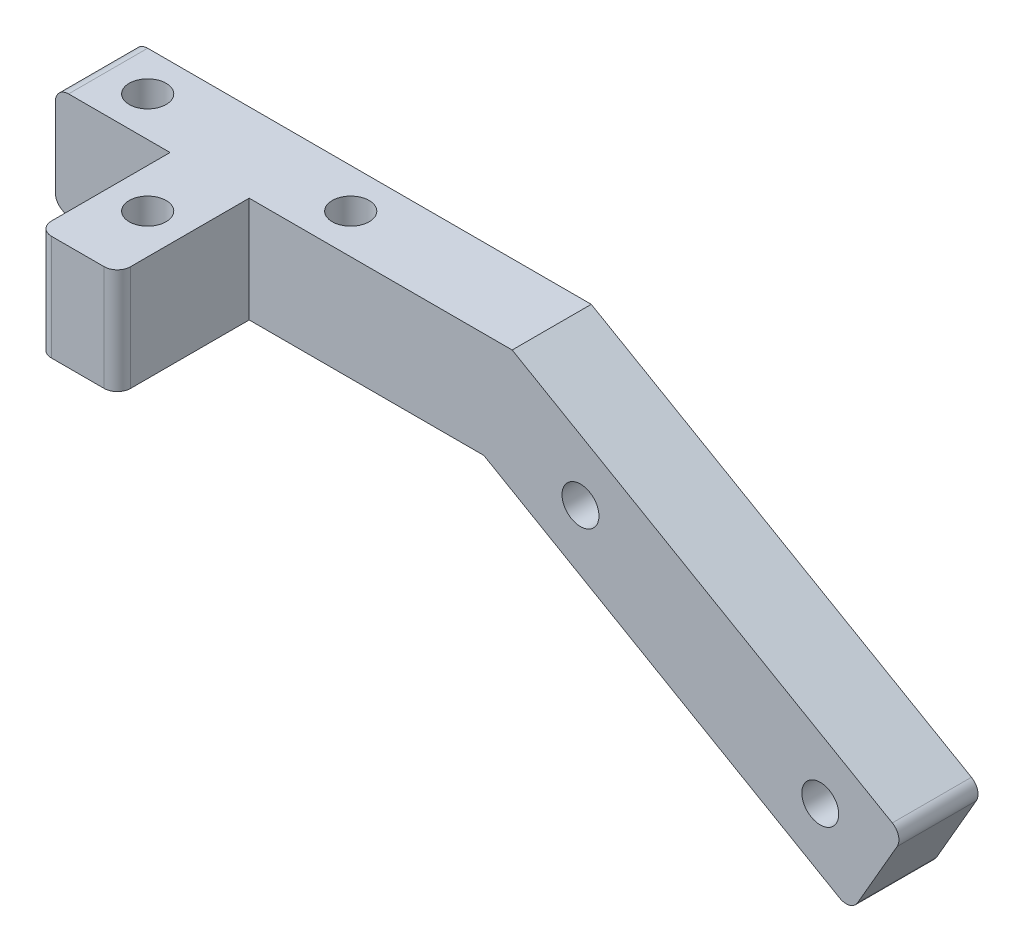
SolidWorks part; units mm, degrees
material "Copper"
ref_plane "Front Plane" through (0, 0, 0) normal (0, 0, 1) x (1, 0, 0)
ref_plane "Top Plane" through (0, 0, 0) normal (0, 1, 0) x (1, 0, 0)
ref_plane "Right Plane" through (0, 0, 0) normal (1, 0, 0) x (0, 0, -1)
sketch "Sketch1" plane through (0, 0, 0) normal (0, 0, 1) x (1, 0, 0)
  line L0 (0, 0) -> (0, 10.16)
  line L1 (0, 10.16) -> (43.9974, 10.16)
  line L2 (43.9974, 10.16) -> (81.7148, -11.6162)
  line L3 (81.7148, -11.6162) -> (76.6348, -20.415)
  line L4 (76.6348, -20.415) -> (41.275, 0)
  line L5 (41.275, 0) -> (0, 0)
  circle A0 centre (50.5786, 0.4944) radius 1.778
  circle A1 centre (73.6755, -12.8406) radius 1.778
  dimension "D4" = 26.67
  dimension "D5" = 3.556
  dimension "D6" = 3.556
  dimension "D1" = 10.16
  dimension "D2" = 10.16
  dimension "D3" = 41.275
  dimension "D7" = 5.08
  dimension "D8" = 5.08
  dimension "D9" = 6.35
  dimension "D10" = 150
extrude "Boss-Extrude1" add sketch "Sketch1" along normal blind 7.62
sketch "Sketch2" plane through (0, 10.16, 0) normal (0, 1, 0) x (1, 0, 0)
  line L0 (43.9974, -7.62) -> (0, -7.62) construction
  line L1 (0, -7.62) -> (0, 0) construction
  circle A0 centre (5.08, -3.81) radius 1.778
  circle A1 centre (24.638, -3.81) radius 1.778
  dimension "D1" = 3.556
  dimension "D2" = 3.556
  dimension "D3" = 19.558
  dimension "D4" = 3.81
  dimension "D5" = 3.81
  dimension "D6" = 5.08
extrude "Cut-Extrude1" cut sketch "Sketch2" against normal blind 10.16
sketch "Sketch3" plane through (0, 10.16, 0) normal (0, 1, 0) x (1, 0, 0)
  line L0 (43.9974, -7.62) -> (0, -7.62) construction
  line L1 (11.049, -7.62) -> (18.669, -7.62)
  line L2 (11.049, -7.62) -> (11.049, -20.32)
  line L3 (11.049, -20.32) -> (18.669, -20.32)
  line L4 (18.669, -7.62) -> (18.669, -20.32)
  circle A0 centre (5.08, -3.81) radius 1.778 construction
  circle A1 centre (14.859, -13.589) radius 1.778
  point P8 (14.859, -7.62)
  dimension "D3" = 9.779
  dimension "D4" = 3.556
  dimension "D1" = 7.62
  dimension "D2" = 12.7
  dimension "D5" = 9.779
  dimension "D6" = 9.779
extrude "Boss-Extrude2" add sketch "Sketch3" against normal blind 10.16
fillet "Fillet1" radius 1.27 6 edges at (0, 10.16, 3.81) (81.7148, -11.6162, 3.81) (76.6348, -20.415, 3.81) (0, 0, 3.81) (18.669, 5.08, 20.32) (11.049, 5.08, 20.32)
